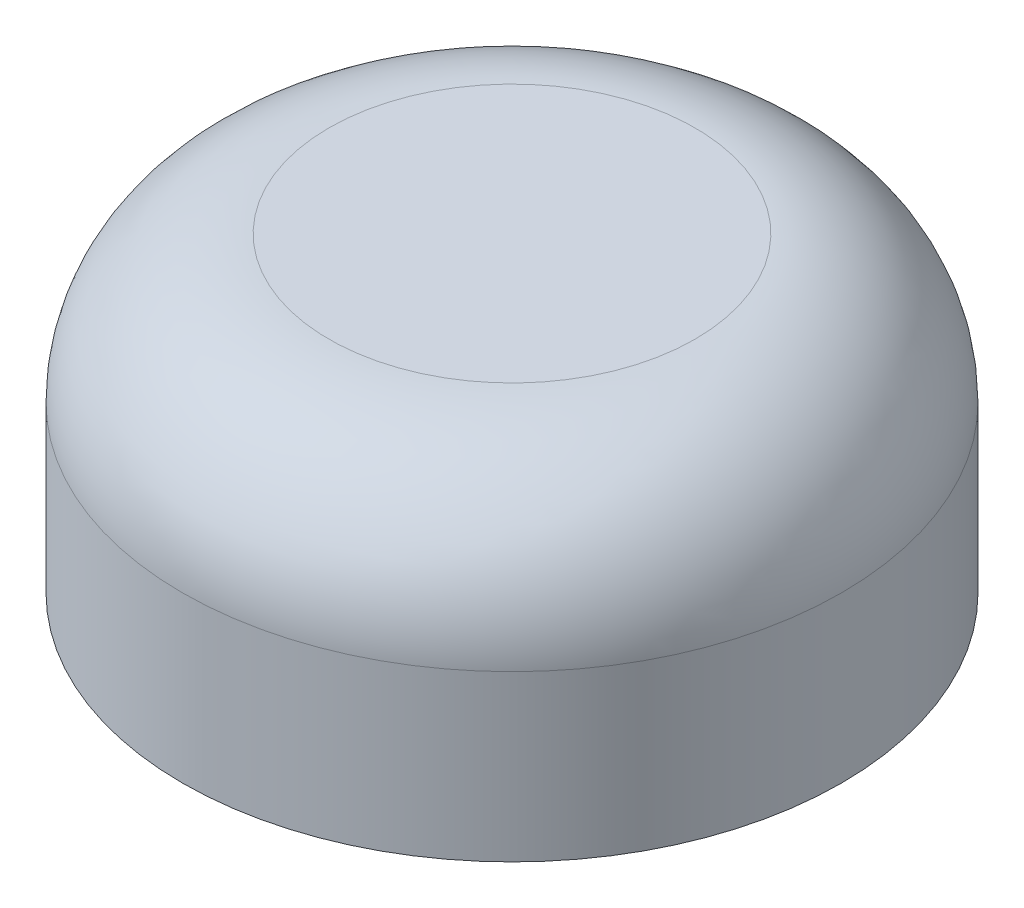
SolidWorks part; units mm, degrees
ref_plane "Piano frontale" through (0, 0, 0) normal (0, 0, 1) x (1, 0, 0)
ref_plane "Piano superiore" through (0, 0, 0) normal (0, 1, 0) x (1, 0, 0)
ref_plane "Piano destro" through (0, 0, 0) normal (1, 0, 0) x (0, 0, -1)
sketch "Schizzo1" plane through (0, 0, 0) normal (0, 0, 1) x (1, 0, 0)
  line L6 (0, 0) -> (1.5, 0)
  line L7 (1.5, 0) -> (1.5, -2.5)
  line L8 (1.5, -2.5) -> (4.5, -2.5)
  line L9 (4.5, -2.5) -> (4.5, -0.25)
  line L10 (2.5, 1.75) -> (0, 1.75)
  line L11 (0, 1.75) -> (0, 0)
  arc A0 (4.5, -0.25) -> (2.5, 1.75) centre (2.5, -0.25) ccw
  dimension "D5" = 2
  dimension "D1" = 1.5
  dimension "D2" = 3
  dimension "D3" = 2.5
  dimension "D4" = 1.75
revolve "Rivoluzione1" add sketch "Schizzo1" angle 360 about L11
